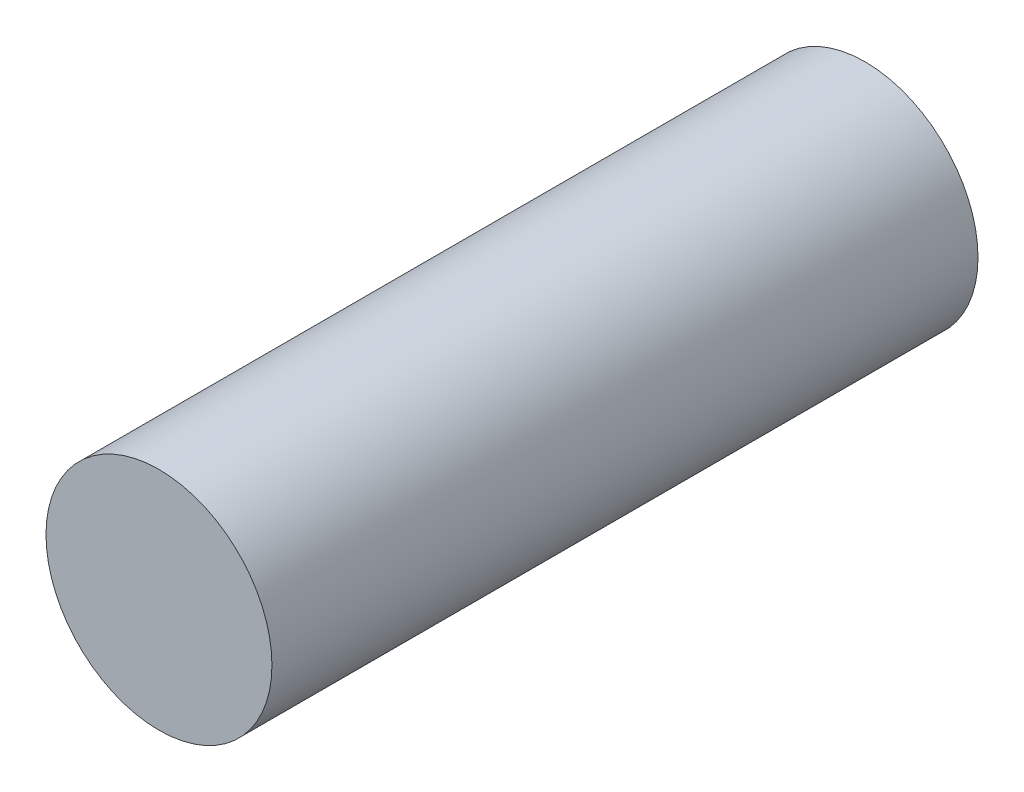
SolidWorks part; units mm, degrees
material "1023 Carbon Steel Sheet (SS)"
ref_plane "Front Plane" through (0, 0, 0) normal (0, 0, 1) x (1, 0, 0)
ref_plane "Top Plane" through (0, 0, 0) normal (0, 1, 0) x (1, 0, 0)
ref_plane "Right Plane" through (0, 0, 0) normal (1, 0, 0) x (0, 0, -1)
sketch "Sketch1" plane through (0, 0, 0) normal (0, 0, 1) x (1, 0, 0)
  circle A0 centre (0, 0) radius 4
  dimension "D1" = 8
extrude "Boss-Extrude1" add sketch "Sketch1" along normal blind 25
